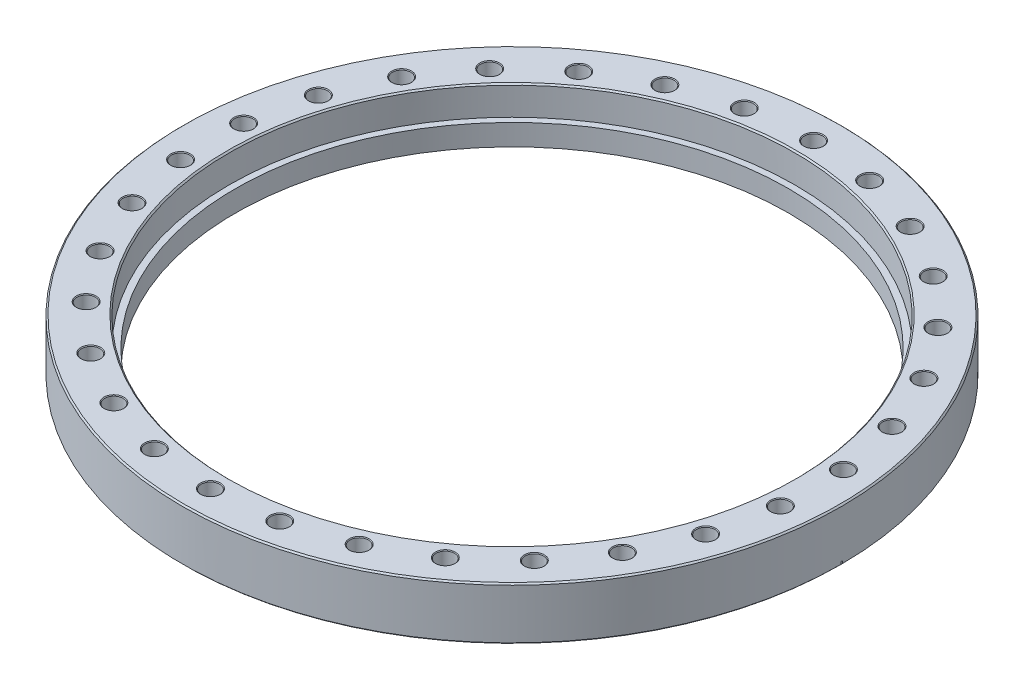
SolidWorks part; units mm, degrees
ref_plane "Front Plane" through (0, 0, 0) normal (0, 0, 1) x (1, 0, 0)
ref_plane "Top Plane" through (0, 0, 0) normal (0, 1, 0) x (1, 0, 0)
ref_plane "Right Plane" through (0, 0, 0) normal (1, 0, 0) x (0, 0, -1)
sketch "Sketch1" plane through (0, 0, 0) normal (0, 1, 0) x (1, 0, 0)
  circle A0 centre (0, 0) radius 177.8
  circle A1 centre (0, 0) radius 149.225
  dimension "D1" = 355.6
  dimension "D2" = 298.45
extrude "Boss-Extrude1" add sketch "Sketch1" along normal blind 28.448
sketch "Sketch2" plane through (0, 28.448, 0) normal (0, -1, 0) x (-1, 0, 0)
  circle A0 centre (0, 0) radius 152.654
  dimension "D1" = 305.308
extrude "Cut-Extrude1" cut sketch "Sketch2" along normal blind 15.748
chamfer "Chamfer1" distance 0.762 angle 45 3 edges at (0, 0, 177.8) (0, 28.448, 177.8) (0, 28.448, -152.654)
sketch "Sketch4" plane through (0, 0, 0) normal (0, 0, 1) x (1, 0, 0)
  line L0 (-156.845, 0) -> (-156.845, 1.816)
  line L1 (-156.845, 1.816) -> (-153.67, 0.6604)
  line L2 (-153.67, 0.6604) -> (-153.67, 1.27)
  line L3 (-153.67, 1.27) -> (0, 1.27)
  line L5 (0, 1.27) -> (0, 0)
  line L6 (0, 0) -> (-156.845, 0)
  dimension "D2" = 156.845
  dimension "D3" = 153.67
  dimension "D4" = 1.27
  dimension "D5" = 1.816
  dimension "D6" = 0.6096
revolve "Cut-Revolve1" cut sketch "Sketch4" angle 360 about axis through (0, 28.448, 0) along (0, -1, 0)
sketch "Sketch3" plane through (0, 28.448, 0) normal (0, 1, 0) x (1, 0, 0)
  line L1 (0, 0) -> (0, 162.687) construction
  circle A0 centre (0, 162.687) radius 4.953
  dimension "D2" = 9.906
  dimension "D1" = 162.687
extrude "Cut-Extrude2" cut sketch "Sketch3" against normal through all
chamfer "Chamfer2" distance 0.381 angle 45 2 edges at (0, 28.448, -157.734) (0, 0, -157.734)
pattern_circular "CirPattern1" count 30 over 360 about axis through (0, 0, 0) along (0, 1, 0) of "Cut-Extrude2", "Chamfer2"
sketch "Sketch5" plane through (0, 0, 0) normal (0, 0, 1) x (1, 0, 0)
  line L0 (-155.4579, 0.8937) -> (-177.8, 2.0646)
  line L1 (-177.8, 2.0646) -> (-177.8, -7.2535)
  line L2 (-177.8, -7.2535) -> (-155.4579, -7.2535)
  line L3 (0, -7.2535) -> (-155.4579, 0.8937) construction
  line L4 (-155.4579, 0.8937) -> (-155.4579, -7.2535)
  line L5 (-155.4579, -7.2535) -> (0, -7.2535) construction
  line L6 (155.4579, 0.8937) -> (155.4579, -7.2535)
  line L7 (177.8, -7.2535) -> (155.4579, -7.2535)
  line L8 (0, -7.2535) -> (0, 0) construction
  line L9 (177.8, 2.0646) -> (177.8, -7.2535)
  line L10 (155.4579, 0.8937) -> (177.8, 2.0646)
  dimension "D1" = 7.2535
  dimension "D3" = 3
extrude "Cut-Extrude3" cut sketch "Sketch5" against normal mid plane 0.762
